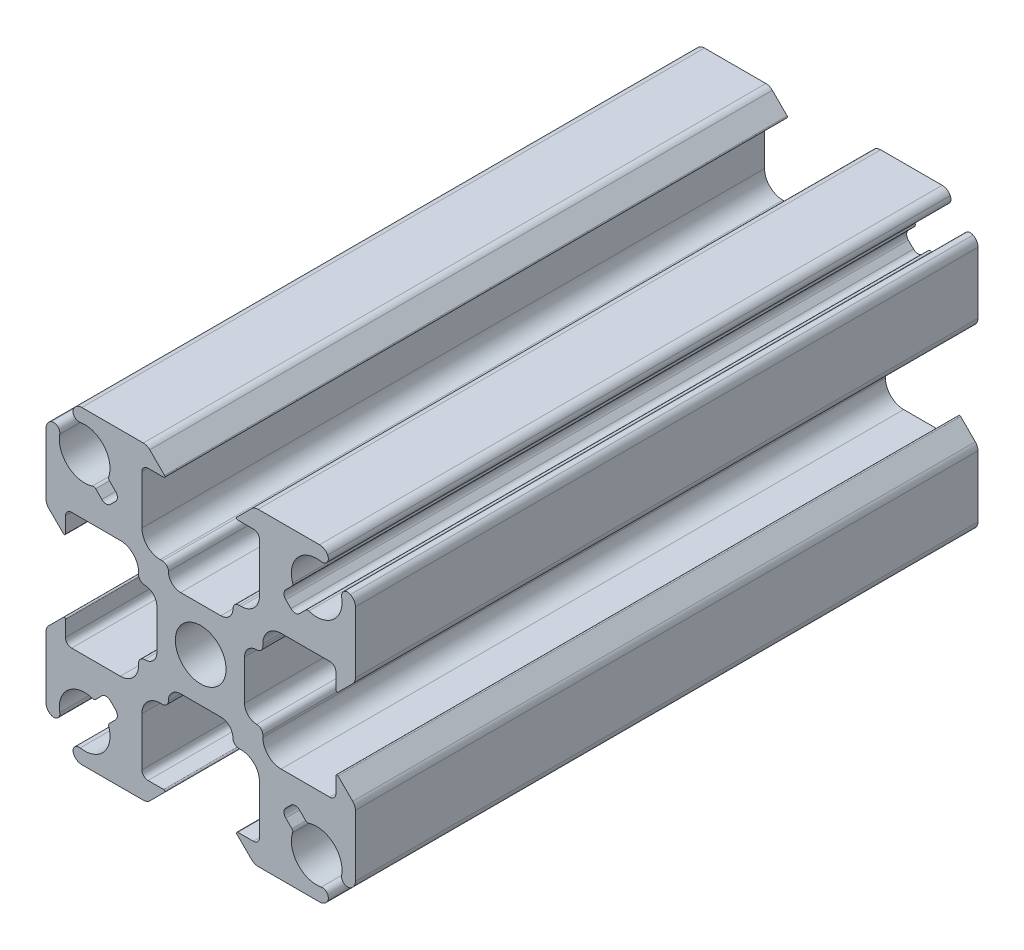
SolidWorks part; units mm, degrees
ref_plane "Front Plane" through (0, 0, 0) normal (0, 0, 1) x (1, 0, 0)
ref_plane "Top Plane" through (0, 0, 0) normal (0, 1, 0) x (1, 0, 0)
ref_plane "Right Plane" through (0, 0, 0) normal (1, 0, 0) x (0, 0, -1)
ref_plane "Plane1" through (0, 0, 0) normal (0, 0, -1) x (-1, 0, 0)
sketch "Sketch1" plane through (0, 0, 0) normal (0, 0, -1) x (-1, 0, 0)
  line L0 (-7.4885, 8.6199) -> (-6.9856, 8.117)
  line L1 (-6.9856, 7.4099) -> (-7.4099, 6.9856)
  line L2 (-8.117, 6.9856) -> (-8.6199, 7.4885)
  line L3 (-12.7, 9.7594) -> (-12.7, 4.7107)
  line L4 (-12.4803, 4.1803) -> (-11.2707, 2.9707)
  line L5 (-11.1, 3.0414) -> (-11.1, 4.325)
  line L6 (-10.6, 4.825) -> (-6.6, 4.825)
  line L7 (-5.1, 3.325) -> (-5.1, 3.15)
  line L8 (-3.6, 1.65) -> (-3.6, -1.65)
  line L9 (-5.1, -3.15) -> (-5.1, -3.325)
  line L10 (-6.6, -4.825) -> (-10.6, -4.825)
  line L11 (-11.1, -4.325) -> (-11.1, -3.0414)
  line L12 (-11.2707, -2.9707) -> (-12.4803, -4.1803)
  line L13 (-12.7, -4.7107) -> (-12.7, -9.7594)
  line L14 (-8.6199, -7.4885) -> (-8.117, -6.9856)
  line L15 (-7.4099, -6.9856) -> (-6.9856, -7.4099)
  line L16 (-6.9856, -8.117) -> (-7.4885, -8.6199)
  line L17 (-9.7594, -12.7) -> (-4.7107, -12.7)
  line L18 (-4.1803, -12.4803) -> (-2.9707, -11.2707)
  line L19 (-3.0414, -11.1) -> (-4.325, -11.1)
  line L20 (-4.825, -10.6) -> (-4.825, -6.6)
  line L21 (-3.325, -5.1) -> (-3.15, -5.1)
  line L22 (-1.65, -3.6) -> (1.65, -3.6)
  line L23 (3.15, -5.1) -> (3.325, -5.1)
  line L24 (4.825, -6.6) -> (4.825, -10.6)
  line L25 (4.325, -11.1) -> (3.0414, -11.1)
  line L26 (2.9707, -11.2707) -> (4.1803, -12.4803)
  line L27 (4.7107, -12.7) -> (9.7594, -12.7)
  line L28 (7.4885, -8.6199) -> (6.9856, -8.117)
  line L29 (6.9856, -7.4099) -> (7.4099, -6.9856)
  line L30 (8.117, -6.9856) -> (8.6199, -7.4885)
  line L31 (12.7, -9.7594) -> (12.7, -4.7107)
  line L32 (12.4803, -4.1803) -> (11.2707, -2.9707)
  line L33 (11.1, -3.0414) -> (11.1, -4.325)
  line L34 (10.6, -4.825) -> (6.6, -4.825)
  line L35 (5.1, -3.325) -> (5.1, -3.15)
  line L36 (3.6, -1.65) -> (3.6, 1.65)
  line L37 (5.1, 3.15) -> (5.1, 3.325)
  line L38 (6.6, 4.825) -> (10.6, 4.825)
  line L39 (11.1, 4.325) -> (11.1, 3.0414)
  line L40 (11.2707, 2.9707) -> (12.4803, 4.1803)
  line L41 (12.7, 4.7107) -> (12.7, 9.7594)
  line L42 (8.6199, 7.4885) -> (8.117, 6.9856)
  line L43 (7.4099, 6.9856) -> (6.9856, 7.4099)
  line L44 (6.9856, 8.117) -> (7.4885, 8.6199)
  line L45 (9.7594, 12.7) -> (4.7107, 12.7)
  line L46 (4.1803, 12.4803) -> (2.9707, 11.2707)
  line L47 (3.0414, 11.1) -> (4.325, 11.1)
  line L48 (4.825, 10.6) -> (4.825, 6.6)
  line L49 (3.325, 5.1) -> (3.15, 5.1)
  line L50 (1.65, 3.6) -> (-1.65, 3.6)
  line L51 (-3.15, 5.1) -> (-3.325, 5.1)
  line L52 (-4.825, 6.6) -> (-4.825, 10.6)
  line L53 (-4.325, 11.1) -> (-3.0414, 11.1)
  line L54 (-2.9707, 11.2707) -> (-4.1803, 12.4803)
  line L55 (-4.7107, 12.7) -> (-9.7594, 12.7)
  circle A0 centre (0, 0) radius 2.08
  arc A1 (-9.7594, 12.7) -> (-10.4266, 12.2927) centre (-9.7594, 11.95) ccw
  arc A2 (-10.4266, 12.2927) -> (-9.8933, 11.5721) centre (-9.9818, 12.0642) ccw
  arc A3 (-9.8933, 11.5721) -> (-7.5492, 8.8748) centre (-9.525, 9.525) cw
  arc A4 (-7.5492, 8.8748) -> (-7.4885, 8.6199) centre (-7.3118, 8.7967) ccw
  arc A5 (-6.9856, 8.117) -> (-6.9856, 7.4099) centre (-7.3392, 7.7635) cw
  arc A6 (-7.4099, 6.9856) -> (-8.117, 6.9856) centre (-7.7635, 7.3392) cw
  arc A7 (-8.6199, 7.4885) -> (-8.8748, 7.5492) centre (-8.7967, 7.3118) ccw
  arc A8 (-8.8748, 7.5492) -> (-11.5721, 9.8933) centre (-9.525, 9.525) cw
  arc A9 (-11.5721, 9.8933) -> (-12.2927, 10.4266) centre (-12.0642, 9.9818) ccw
  arc A10 (-12.2927, 10.4266) -> (-12.7, 9.7594) centre (-11.95, 9.7594) ccw
  arc A11 (-12.7, 4.7107) -> (-12.4803, 4.1803) centre (-11.95, 4.7107) ccw
  arc A12 (-11.2707, 2.9707) -> (-11.1, 3.0414) centre (-11.2, 3.0414) ccw
  arc A13 (-11.1, 4.325) -> (-10.6, 4.825) centre (-10.6, 4.325) cw
  arc A14 (-6.6, 4.825) -> (-5.1, 3.325) centre (-6.6, 3.325) cw
  arc A15 (-5.1, 3.15) -> (-4.6, 2.65) centre (-4.6, 3.15) ccw
  arc A16 (-4.6, 2.65) -> (-3.6, 1.65) centre (-4.6, 1.65) cw
  arc A17 (-3.6, -1.65) -> (-4.6, -2.65) centre (-4.6, -1.65) cw
  arc A18 (-4.6, -2.65) -> (-5.1, -3.15) centre (-4.6, -3.15) ccw
  arc A19 (-5.1, -3.325) -> (-6.6, -4.825) centre (-6.6, -3.325) cw
  arc A20 (-10.6, -4.825) -> (-11.1, -4.325) centre (-10.6, -4.325) cw
  arc A21 (-11.1, -3.0414) -> (-11.2707, -2.9707) centre (-11.2, -3.0414) ccw
  arc A22 (-12.4803, -4.1803) -> (-12.7, -4.7107) centre (-11.95, -4.7107) ccw
  arc A23 (-12.7, -9.7594) -> (-12.2927, -10.4266) centre (-11.95, -9.7594) ccw
  arc A24 (-12.2927, -10.4266) -> (-11.5721, -9.8933) centre (-12.0642, -9.9818) ccw
  arc A25 (-11.5721, -9.8933) -> (-8.8748, -7.5492) centre (-9.525, -9.525) cw
  arc A26 (-8.8748, -7.5492) -> (-8.6199, -7.4885) centre (-8.7967, -7.3118) ccw
  arc A27 (-8.117, -6.9856) -> (-7.4099, -6.9856) centre (-7.7635, -7.3392) cw
  arc A28 (-6.9856, -7.4099) -> (-6.9856, -8.117) centre (-7.3392, -7.7635) cw
  arc A29 (-7.4885, -8.6199) -> (-7.5492, -8.8748) centre (-7.3118, -8.7967) ccw
  arc A30 (-7.5492, -8.8748) -> (-9.8933, -11.5721) centre (-9.525, -9.525) cw
  arc A31 (-9.8933, -11.5721) -> (-10.4266, -12.2927) centre (-9.9818, -12.0642) ccw
  arc A32 (-10.4266, -12.2927) -> (-9.7594, -12.7) centre (-9.7594, -11.95) ccw
  arc A33 (-4.7107, -12.7) -> (-4.1803, -12.4803) centre (-4.7107, -11.95) ccw
  arc A34 (-2.9707, -11.2707) -> (-3.0414, -11.1) centre (-3.0414, -11.2) ccw
  arc A35 (-4.325, -11.1) -> (-4.825, -10.6) centre (-4.325, -10.6) cw
  arc A36 (-4.825, -6.6) -> (-3.325, -5.1) centre (-3.325, -6.6) cw
  arc A37 (-3.15, -5.1) -> (-2.65, -4.6) centre (-3.15, -4.6) ccw
  arc A38 (-2.65, -4.6) -> (-1.65, -3.6) centre (-1.65, -4.6) cw
  arc A39 (1.65, -3.6) -> (2.65, -4.6) centre (1.65, -4.6) cw
  arc A40 (2.65, -4.6) -> (3.15, -5.1) centre (3.15, -4.6) ccw
  arc A41 (3.325, -5.1) -> (4.825, -6.6) centre (3.325, -6.6) cw
  arc A42 (4.825, -10.6) -> (4.325, -11.1) centre (4.325, -10.6) cw
  arc A43 (3.0414, -11.1) -> (2.9707, -11.2707) centre (3.0414, -11.2) ccw
  arc A44 (4.1803, -12.4803) -> (4.7107, -12.7) centre (4.7107, -11.95) ccw
  arc A45 (9.7594, -12.7) -> (10.4266, -12.2927) centre (9.7594, -11.95) ccw
  arc A46 (10.4266, -12.2927) -> (9.8933, -11.5721) centre (9.9818, -12.0642) ccw
  arc A47 (9.8933, -11.5721) -> (7.5492, -8.8748) centre (9.525, -9.525) cw
  arc A48 (7.5492, -8.8748) -> (7.4885, -8.6199) centre (7.3118, -8.7967) ccw
  arc A49 (6.9856, -8.117) -> (6.9856, -7.4099) centre (7.3392, -7.7635) cw
  arc A50 (7.4099, -6.9856) -> (8.117, -6.9856) centre (7.7635, -7.3392) cw
  arc A51 (8.6199, -7.4885) -> (8.8748, -7.5492) centre (8.7967, -7.3118) ccw
  arc A52 (8.8748, -7.5492) -> (11.5721, -9.8933) centre (9.525, -9.525) cw
  arc A53 (11.5721, -9.8933) -> (12.2927, -10.4266) centre (12.0642, -9.9818) ccw
  arc A54 (12.2927, -10.4266) -> (12.7, -9.7594) centre (11.95, -9.7594) ccw
  arc A55 (12.7, -4.7107) -> (12.4803, -4.1803) centre (11.95, -4.7107) ccw
  arc A56 (11.2707, -2.9707) -> (11.1, -3.0414) centre (11.2, -3.0414) ccw
  arc A57 (11.1, -4.325) -> (10.6, -4.825) centre (10.6, -4.325) cw
  arc A58 (6.6, -4.825) -> (5.1, -3.325) centre (6.6, -3.325) cw
  arc A59 (5.1, -3.15) -> (4.6, -2.65) centre (4.6, -3.15) ccw
  arc A60 (4.6, -2.65) -> (3.6, -1.65) centre (4.6, -1.65) cw
  arc A61 (3.6, 1.65) -> (4.6, 2.65) centre (4.6, 1.65) cw
  arc A62 (4.6, 2.65) -> (5.1, 3.15) centre (4.6, 3.15) ccw
  arc A63 (5.1, 3.325) -> (6.6, 4.825) centre (6.6, 3.325) cw
  arc A64 (10.6, 4.825) -> (11.1, 4.325) centre (10.6, 4.325) cw
  arc A65 (11.1, 3.0414) -> (11.2707, 2.9707) centre (11.2, 3.0414) ccw
  arc A66 (12.4803, 4.1803) -> (12.7, 4.7107) centre (11.95, 4.7107) ccw
  arc A67 (12.7, 9.7594) -> (12.2927, 10.4266) centre (11.95, 9.7594) ccw
  arc A68 (12.2927, 10.4266) -> (11.5721, 9.8933) centre (12.0642, 9.9818) ccw
  arc A69 (11.5721, 9.8933) -> (8.8748, 7.5492) centre (9.525, 9.525) cw
  arc A70 (8.8748, 7.5492) -> (8.6199, 7.4885) centre (8.7967, 7.3118) ccw
  arc A71 (8.117, 6.9856) -> (7.4099, 6.9856) centre (7.7635, 7.3392) cw
  arc A72 (6.9856, 7.4099) -> (6.9856, 8.117) centre (7.3392, 7.7635) cw
  arc A73 (7.4885, 8.6199) -> (7.5492, 8.8748) centre (7.3118, 8.7967) ccw
  arc A74 (7.5492, 8.8748) -> (9.8933, 11.5721) centre (9.525, 9.525) cw
  arc A75 (9.8933, 11.5721) -> (10.4266, 12.2927) centre (9.9818, 12.0642) ccw
  arc A76 (10.4266, 12.2927) -> (9.7594, 12.7) centre (9.7594, 11.95) ccw
  arc A77 (4.7107, 12.7) -> (4.1803, 12.4803) centre (4.7107, 11.95) ccw
  arc A78 (2.9707, 11.2707) -> (3.0414, 11.1) centre (3.0414, 11.2) ccw
  arc A79 (4.325, 11.1) -> (4.825, 10.6) centre (4.325, 10.6) cw
  arc A80 (4.825, 6.6) -> (3.325, 5.1) centre (3.325, 6.6) cw
  arc A81 (3.15, 5.1) -> (2.65, 4.6) centre (3.15, 4.6) ccw
  arc A82 (2.65, 4.6) -> (1.65, 3.6) centre (1.65, 4.6) cw
  arc A83 (-1.65, 3.6) -> (-2.65, 4.6) centre (-1.65, 4.6) cw
  arc A84 (-2.65, 4.6) -> (-3.15, 5.1) centre (-3.15, 4.6) ccw
  arc A85 (-3.325, 5.1) -> (-4.825, 6.6) centre (-3.325, 6.6) cw
  arc A86 (-4.825, 10.6) -> (-4.325, 11.1) centre (-4.325, 10.6) cw
  arc A87 (-3.0414, 11.1) -> (-2.9707, 11.2707) centre (-3.0414, 11.2) ccw
  arc A88 (-4.1803, 12.4803) -> (-4.7107, 12.7) centre (-4.7107, 11.95) ccw
extrude "Boss-Extrude1" add sketch "Sketch1" against normal mid plane 51.1156
